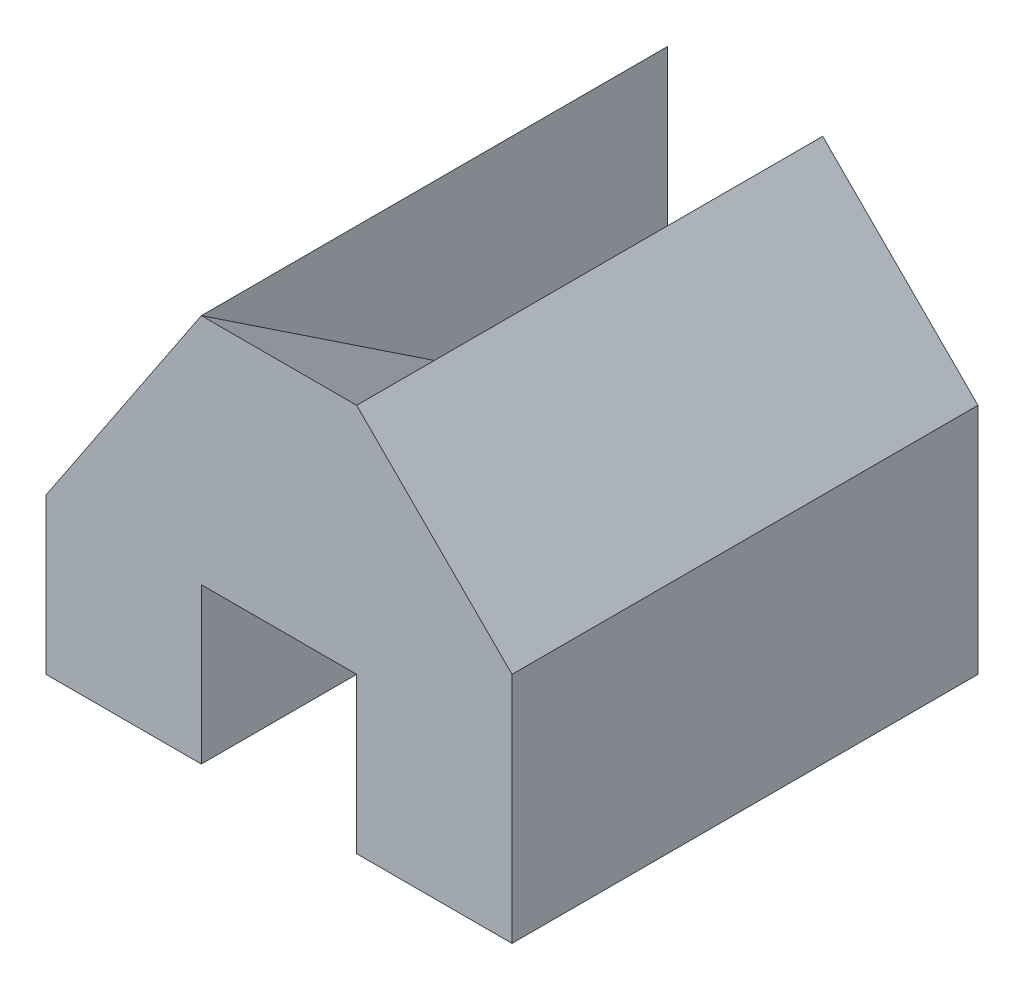
SolidWorks part; units mm, degrees
ref_plane "Front" through (0, 0, 0) normal (0, 0, 1) x (1, 0, 0)
ref_plane "Top" through (0, 0, 0) normal (0, 1, 0) x (1, 0, 0)
ref_plane "Right" through (0, 0, 0) normal (1, 0, 0) x (0, 0, -1)
sketch "Sketch1" plane through (0, 0, 0) normal (0, 1, 0) x (1, 0, 0)
  line L1 (-3, -3) -> (3, -3)
  line L2 (-3, -3) -> (-3, 3)
  line L3 (-3, 3) -> (3, 3)
  line L4 (3, -3) -> (3, 3)
  line L5 (-3, -3) -> (3, 3) construction
  line L6 (-3, 3) -> (3, -3) construction
  point P0 (0, 0)
  dimension "D1" = 6
  dimension "D2" = 6
extrude "Boss-Extrude1" add sketch "Sketch1" along normal blind 5
sketch "Sketch9" plane through (0, 0, 0) normal (1, 0, 0) x (0, 0, -1)
  line L0 (-3, 5) -> (3, 1)
  line L1 (-3, 5) -> (-3, 0) construction
  line L2 (-3, 2) -> (3, 0)
  line L7 (-3, 0) -> (3, 0)
  line L8 (-3, 5) -> (-3, 0)
  line L9 (3, 5) -> (-3, 5)
  line L10 (3, 0) -> (3, 5)
  line L11 (-3, 0) -> (3, 0)
  line L12 (-3, 5) -> (-3, 0)
  line L13 (3, 5) -> (-3, 5)
  line L14 (3, 0) -> (3, 5)
  dimension "D2" = 2
  dimension "D3" = 4
  dimension "D1" = 0
extrude "Cut-Extrude8" cut sketch "Sketch9" against normal mid plane 2
sketch "Sketch10" plane through (0, 0, 3) normal (0, 0, 1) x (1, 0, 0)
  line L0 (-1, 5) -> (-3, 2)
  line L1 (-3, 5) -> (-3, 0) construction
  line L2 (1, 5) -> (3, 3)
  line L3 (3, 5) -> (3, 0) construction
  line L14 (-1, 0) -> (-1, 2)
  line L15 (-1, 2) -> (1, 2)
  line L16 (1, 2) -> (1, 0)
  line L17 (1, 0) -> (3, 0)
  line L18 (3, 0) -> (3, 5)
  line L19 (3, 5) -> (1, 5)
  line L20 (1, 5) -> (-1, 5)
  line L21 (-1, 5) -> (-3, 5)
  line L22 (-3, 5) -> (-3, 0)
  line L23 (-3, 0) -> (-1, 0)
  line L24 (-1, 0) -> (-1, 2)
  line L25 (-1, 2) -> (1, 2)
  line L26 (1, 2) -> (1, 0)
  line L27 (1, 0) -> (3, 0)
  line L28 (3, 0) -> (3, 5)
  line L29 (3, 5) -> (1, 5)
  line L30 (1, 5) -> (-1, 5)
  line L31 (-1, 5) -> (-3, 5)
  line L32 (-3, 5) -> (-3, 0)
  line L33 (-3, 0) -> (-1, 0)
  line M17 (3, 0) -> (3, 5)
  line M18 (3, 5) -> (1, 5)
  line M20 (-1, 5) -> (-3, 5)
  line M21 (-3, 5) -> (-3, 0)
  dimension "D1" = 3
  dimension "D2" = 2
  dimension "D3" = 0
extrude "Cut-Extrude11" cut sketch "Sketch10" against normal blind 12 contours L0 M20 M21 | L2 M18 M17
